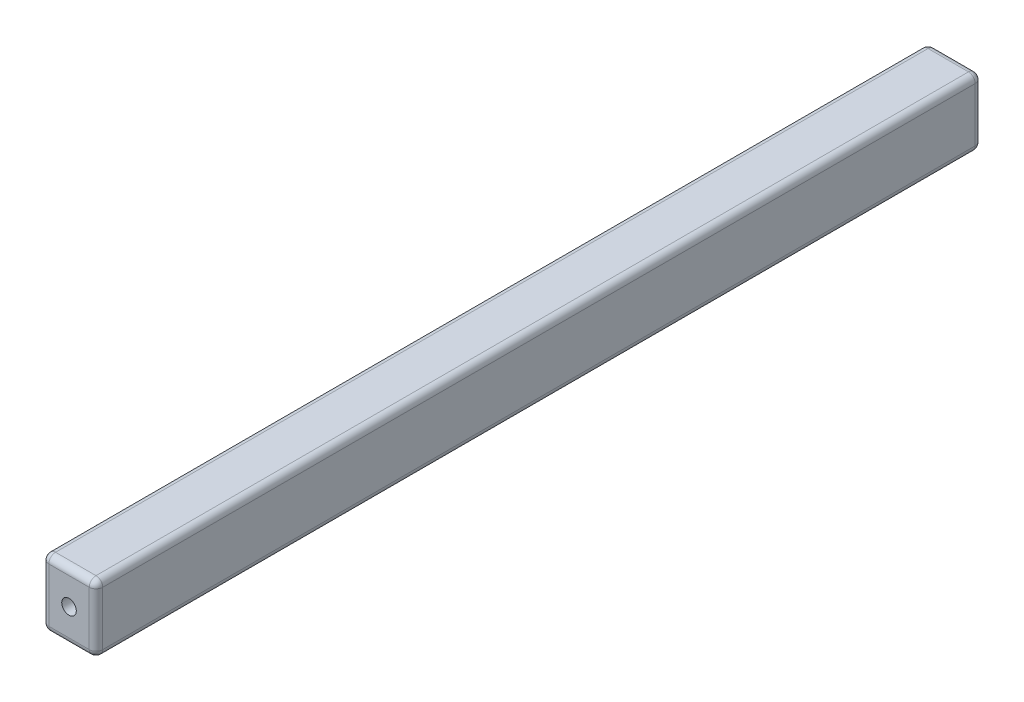
SolidWorks part; units mm, degrees
ref_plane "Alzado" through (0, 0, 0) normal (0, 0, 1) x (1, 0, 0)
ref_plane "Planta" through (0, 0, 0) normal (0, 1, 0) x (1, 0, 0)
ref_plane "Vista lateral" through (0, 0, 0) normal (1, 0, 0) x (0, 0, -1)
sketch "Croquis1" plane through (0, 0, 0) normal (0, 0, 1) x (1, 0, 0)
  line L1 (20, -25) -> (-20, -25)
  line L2 (20, -25) -> (20, 25)
  line L3 (20, 25) -> (-20, 25)
  line L4 (-20, -25) -> (-20, 25)
  line L5 (20, -25) -> (-20, 25) construction
  line L6 (20, 25) -> (-20, -25) construction
  point P0 (0, 0)
  dimension "D1" = 50
  dimension "D2" = 40
extrude "Saliente-Extruir1" add sketch "Croquis1" along normal mid plane 656.9
fillet "Redondeo1" radius 5 12 edges at (-20, -25, 0) (0, -25, -328.45) (-20, 0, -328.45) (0, -25, 328.45) (-20, 0, 328.45) (20, -25, 0) (20, 0, 328.45) (20, 0, -328.45) (20, 25, 0) (0, 25, 328.45) (-20, 25, 0) (0, 25, -328.45)
sketch "Croquis2" plane through (0, 0, 328.45) normal (0, 0, 1) x (1, 0, 0)
  point P0 (0, 0)
hole_wizard "Taladro roscado M12x1.251" positions "Croquis2" profile "Croquis3" tap size "M12x1.25" standard "Ansi Metric"
sketch "Croquis3" plane through (0, 0, 328.45) normal (1, 0, 0) x (0, -1, 0)
  line L0 (0, 0) -> (0, 13.2446)
  line L1 (0, 13.2446) -> (5.4, 10)
  line L2 (5.4, 10) -> (5.4, 0)
  line L5 (5.4, 0) -> (0, 0)
  line L10 (0, 13.2446) -> (-5.4, 10) construction
  line L11 (0, -6.35) -> (0, 107.95) construction
  dimension "Diámetro de perforador para roscar" = 10.8
  dimension "Profundidad de perforador para roscar" = 10
  dimension "Ángulo de perforador" = 118
mirror "Simetría1" about plane through (0, 0, 0) normal (0, 0, 1) of "Taladro roscado M12x1.251"
